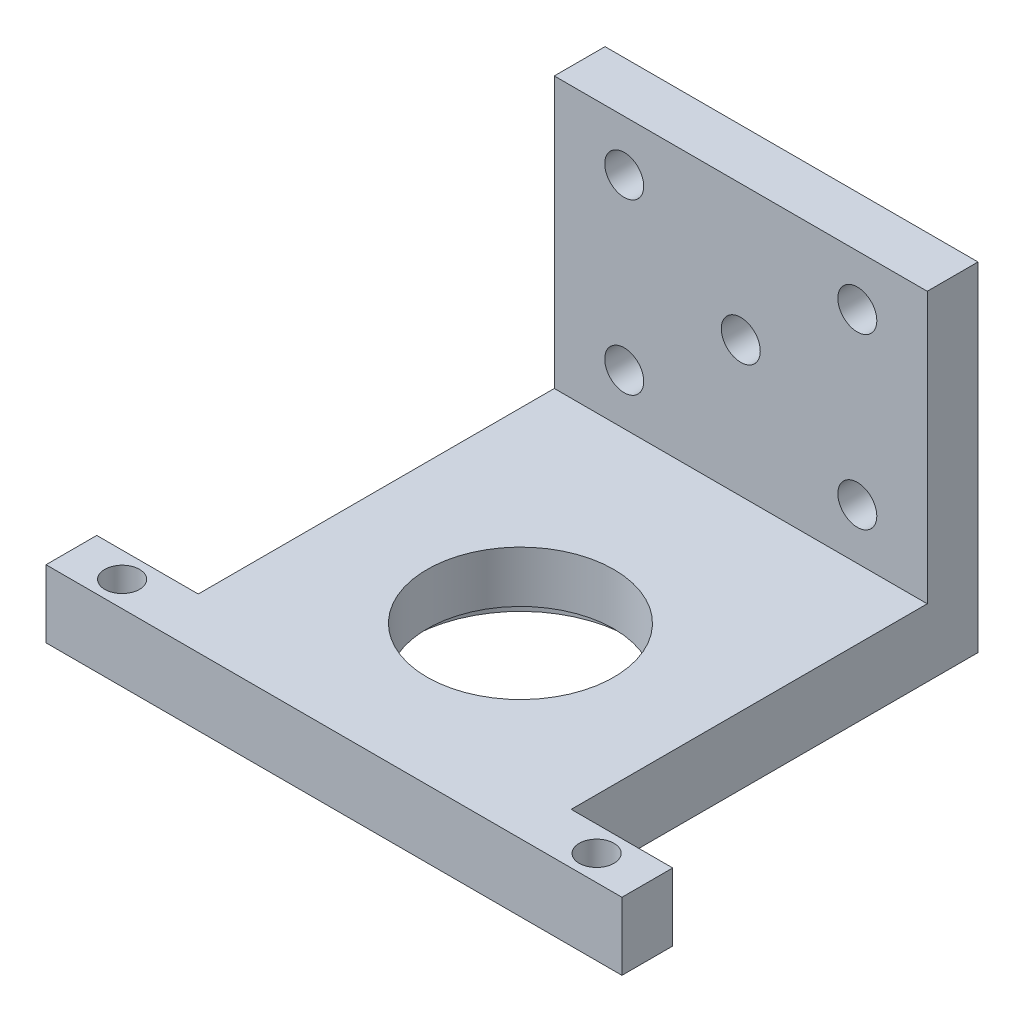
SolidWorks part; units mm, degrees
material "Acrylic (Medium-high impact)"
ref_plane "Front Plane" through (0, 0, 0) normal (0, 0, 1) x (1, 0, 0)
ref_plane "Top Plane" through (0, 0, 0) normal (0, 1, 0) x (1, 0, 0)
ref_plane "Right Plane" through (0, 0, 0) normal (1, 0, 0) x (0, 0, -1)
sketch "Sketch1" plane through (0, 0, 0) normal (0, 1, 0) x (1, 0, 0)
  line L1 (0, 0) -> (35, 0) construction
  line L2 (0, 0) -> (0, 35) construction
  line L3 (0, 35) -> (35, 35) construction
  line L4 (35, 0) -> (35, 35) construction
  line L5 (0, 0) -> (35, 0)
  line L6 (0, 0) -> (0, 42.9375)
  line L7 (0, 42.9375) -> (35, 42.9375)
  line L8 (35, 0) -> (35, 42.9375)
  dimension "D1" = 35
  dimension "D2" = 7.9375
extrude "Boss-Extrude1" add sketch "Sketch1" along normal blind 6.35
sketch "Sketch2" plane through (0, 6.35, 0) normal (0, 1, 0) x (1, 0, 0)
  line L0 (35, 0) -> (35, 42.9375) construction
  line L1 (0, 42.9375) -> (35, 42.9375)
  line L2 (0, 42.9375) -> (0, 38.175)
  line L3 (0, 38.175) -> (35, 38.175)
  line L4 (35, 42.9375) -> (35, 38.175)
  dimension "D1" = 4.7625
extrude "Boss-Extrude2" add sketch "Sketch2" along normal blind 25.4
sketch "Sketch3" plane through (0, 0, 0) normal (0, -1, 0) x (1, 0, 0)
  line L0 (35, -35) -> (0, -35) construction
  line L1 (35, 0) -> (35, -42.9375) construction
  line L2 (0, -42.9375) -> (0, 0) construction
  line L3 (0, -38.175) -> (35, -38.175) construction
  line L4 (35, -35) -> (0, 0) construction
  circle A0 centre (17.5, -17.5) radius 8.763
  dimension "D2" = 17.526
  dimension "D1" = 3.175
extrude "Cut-Extrude1" cut sketch "Sketch3" against normal through all
hole_wizard "CBORE for M2.5 SHCS1" [suppressed] positions "Sketch6" profile "Sketch7" counterbore size "M2.5" standard "ANSI Metric"
sketch "Sketch6" plane through (0, 0, 0) normal (0, -1, 0) x (-1, 0, 0)
  line L1 (-29, 6) -> (-6, 6) construction
  line L2 (-29, 6) -> (-29, 29) construction
  line L3 (-29, 29) -> (-6, 29) construction
  line L4 (-6, 6) -> (-6, 29) construction
  line L5 (-29, 6) -> (-6, 29) construction
  line L6 (-29, 29) -> (-6, 6) construction
  point P1 (-17.5, 17.5)
  point P2 (-6, 29)
  point P27 (-29, 6)
  point P28 (-29, 29)
  point P29 (-6, 6)
  dimension "D1" = 23
sketch "Sketch7" plane through (17.5, 0, -17.5) normal (1, 0, 0) x (0, 0, -1)
  line L0 (0, 0) -> (0, 49.2125)
  line L1 (0, 49.2125) -> (1.35, 49.2125)
  line L3 (1.35, 49.2125) -> (1.35, 2.5)
  line L4 (1.35, 2.5) -> (2.75, 2.5)
  line L5 (2.75, 2.5) -> (2.75, 0)
  line L7 (2.75, 0) -> (0, 0)
  line L11 (0, -6.35) -> (0, 107.95) construction
  dimension "Thru Hole Dia." = 2.7
  dimension "Thru Hole Depth" = 49.2125
  dimension "C'Bore Dia." = 5.5
  dimension "C'Bore Depth" = 2.5
sketch "Sketch8" plane through (0, 0, -38.175) normal (0, 0, 1) x (1, 0, 0)
  line L0 (35, 6.35) -> (0, 31.75) construction
  line L1 (35, 31.75) -> (35, 6.35) construction
  line L2 (41.35, 31.75) -> (-6.35, 31.75) construction
  line L3 (41.35, 31.75) -> (41.35, 6.35) construction
  line L4 (41.35, 6.35) -> (-6.35, 6.35) construction
  line L5 (-6.35, 31.75) -> (-6.35, 6.35) construction
  line L6 (41.35, 31.75) -> (-6.35, 6.35) construction
  line L7 (41.35, 6.35) -> (-6.35, 31.75) construction
  line L8 (35, -3.0382) -> (43.6719, 3.034)
  line L9 (35, 15.7382) -> (43.6719, 9.666)
  line L10 (35, -3.0382) -> (35, 15.7382)
  line L11 (35, 19.05) -> (0, 19.05) construction
  line L12 (0, 31.75) -> (0, 6.35) construction
  line L13 (17.5, 31.75) -> (17.5, 6.35) construction
  line L14 (35, 22.3618) -> (43.6719, 28.434)
  line L15 (35, 41.1382) -> (35, 22.3618)
  line L16 (35, 41.1382) -> (43.6719, 35.066)
  line L17 (0, 41.1382) -> (-8.6719, 35.066)
  line L18 (0, 41.1382) -> (0, 22.3618)
  line L19 (0, 22.3618) -> (-8.6719, 28.434)
  line L20 (0, 15.7382) -> (-8.6719, 9.666)
  line L21 (0, -3.0382) -> (-8.6719, 3.034)
  line L22 (0, -3.0382) -> (0, 15.7382)
  arc A0 (43.6719, 3.034) -> (43.6719, 9.666) centre (41.35, 6.35) ccw
  arc A1 (43.6719, 35.066) -> (43.6719, 28.434) centre (41.35, 31.75) cw
  arc A2 (-8.6719, 35.066) -> (-8.6719, 28.434) centre (-6.35, 31.75) ccw
  arc A3 (-8.6719, 3.034) -> (-8.6719, 9.666) centre (-6.35, 6.35) cw
  point P4 (17.5, 19.05)
  point P20 (17.5, 19.05)
  point P23 (17.5, 19.05)
  dimension "D3" = 8.0962
  dimension "D1" = 25.4
  dimension "D2" = 6.35
  dimension "D4" = 70
extrude "Boss-Extrude3" [suppressed] add sketch "Sketch8" against normal blind 4.7625
hole_wizard "#6 Clearance Hole2" [suppressed] positions "Sketch9" profile "Sketch10" hole size "#6" standard "ANSI Inch"
sketch "Sketch9" [suppressed] plane through (0, 0, -38.175) normal (0, 0, 1) x (1, 0, 0)
  point P0 (41.35, 14.2875)
  point P3 (41.35, 39.6875)
  point P6 (-6.35, 14.2875)
  point P9 (-6.35, 39.6875)
sketch "Sketch10" plane through (41.35, 14.2875, -38.175) normal (1, 0, 0) x (0, -1, 0)
  line L0 (0, 0) -> (0, 4.7625)
  line L1 (0, 4.7625) -> (1.8288, 4.7625)
  line L2 (1.8288, 4.7625) -> (1.8288, 0)
  line L5 (1.8288, 0) -> (0, 0)
  line L11 (0, -6.35) -> (0, 107.95) construction
  dimension "Thru Hole Dia." = 3.6576
  dimension "Thru Hole Depth" = 4.7625
hole_wizard "#6 Clearance Hole1" positions "Sketch11" profile "Sketch12" hole size "#6" standard "ANSI Inch" end condition through all
sketch "Sketch11" plane through (0, 0, -38.175) normal (0, 0, 1) x (1, 0, 0)
  line L0 (35, 6.35) -> (0, 31.75) construction
  line L3 (28.4375, 26.9875) -> (6.5625, 26.9875) construction
  line L4 (28.4375, 26.9875) -> (28.4375, 11.1125) construction
  line L5 (28.4375, 11.1125) -> (6.5625, 11.1125) construction
  line L6 (6.5625, 26.9875) -> (6.5625, 11.1125) construction
  line L7 (28.4375, 26.9875) -> (6.5625, 11.1125) construction
  line L8 (28.4375, 11.1125) -> (6.5625, 26.9875) construction
  point P7 (17.5, 19.05)
  point P8 (6.5625, 11.1125)
  point P59 (28.4375, 26.9875)
  point P65 (28.4375, 11.1125)
  point P68 (6.5625, 26.9875)
  dimension "D1" = 15.875
sketch "Sketch12" plane through (6.5625, 26.9875, -38.175) normal (1, 0, 0) x (0, -1, 0)
  line L0 (0, 0) -> (0, 4.7625)
  line L1 (0, 4.7625) -> (1.8288, 4.7625)
  line L2 (1.8288, 4.7625) -> (1.8288, 0)
  line L5 (1.8288, 0) -> (0, 0)
  line L11 (0, -6.35) -> (0, 107.95) construction
  dimension "Thru Hole Dia." = 3.6576
  dimension "Thru Hole Depth" = 4.7625
sketch "Sketch13" plane through (0, 0, 0) normal (0, -1, 0) x (1, 0, 0)
  circle A0 centre (17.5, -17.5) radius 10.3505
  circle A1 centre (17.5, -17.5) radius 8.763
  dimension "D1" = 20.701
extrude "Cut-Extrude2" cut sketch "Sketch13" against normal blind 1.524
fillet "Fillet1" [suppressed] radius 0.127
fillet "Fillet2" [suppressed] radius 2
sketch "Sketch14" plane through (0, 0, 0) normal (0, -1, 0) x (1, 0, 0)
  line L0 (17.5, -42.9375) -> (17.5, 0) construction
  line L1 (35, -42.9375) -> (0, -42.9375) construction
  line L2 (0, 0) -> (35, 0) construction
  line L3 (0, -42.9375) -> (0, 0) construction
  line L4 (44.525, -4.7625) -> (35, -4.7625)
  line L5 (44.525, -4.7625) -> (44.525, 0)
  line L6 (44.525, 0) -> (35, 0)
  line L7 (-9.525, -4.7625) -> (-9.525, 0)
  line L8 (44.525, -4.7625) -> (35, -3.9232) construction
  line L9 (44.525, 0) -> (35, -0.8393) construction
  line L10 (35, -4.7625) -> (35, 0)
  line L11 (0, -4.7625) -> (0, 0)
  line L12 (0, -4.7625) -> (-9.525, -4.7625)
  line L13 (0, -0.8393) -> (-9.525, 0) construction
  line L14 (0, -3.9232) -> (-9.525, -4.7625) construction
  line L15 (0, 0) -> (-9.525, 0)
  line L16 (35, 0) -> (35, -42.9375) construction
  point P6 (17.5, -2.3812)
  dimension "D1" = 4.7625
  dimension "D2" = 9.525
extrude "Boss-Extrude4" add sketch "Sketch14" against normal blind 6.35
hole_wizard "#4 Clearance Hole1" positions "Sketch15" profile "Sketch16" hole size "#4" standard "ANSI Inch"
sketch "Sketch15" plane through (0, 0, 0) normal (0, -1, 0) x (-1, 0, 0)
  line L0 (-35, 4.7625) -> (-44.525, 0) construction
  line L2 (0, 4.7625) -> (9.525, 0) construction
  point P11 (-39.7625, 2.3813)
  point P13 (4.7625, 2.3813)
sketch "Sketch16" plane through (-4.7625, 0, -2.3813) normal (1, 0, 0) x (0, 0, -1)
  line L0 (0, 0) -> (0, 11.1406)
  line L1 (0, 11.1406) -> (1.6319, 10.16)
  line L2 (1.6319, 10.16) -> (1.6319, 0)
  line L5 (1.6319, 0) -> (0, 0)
  line L10 (0, 11.1406) -> (-1.632, 10.16) construction
  line L11 (0, -6.35) -> (0, 107.95) construction
  dimension "Hole Dia." = 3.2639
  dimension "Hole Depth" = 10.16
  dimension "Drill Angle" = 118
equation "\"hole\"=24"
